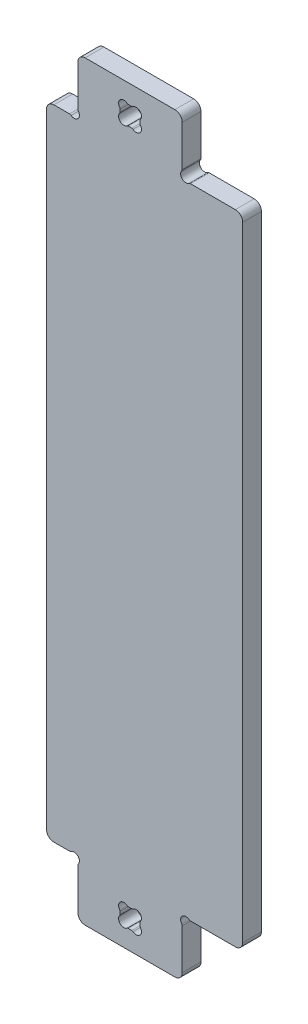
SolidWorks part; units mm, degrees
ref_plane "Plan de face" through (0, 0, 0) normal (0, 0, 1) x (1, 0, 0)
ref_plane "Plan de dessus" through (0, 0, 0) normal (0, 1, 0) x (1, 0, 0)
ref_plane "Plan de droite" through (0, 0, 0) normal (1, 0, 0) x (0, 0, -1)
sketch "Esquisse2" plane through (0, 0, 0) normal (0, 0, 1) x (1, 0, 0)
  line L0 (0, 54) -> (-3.6998, 50.3002) construction
  line L1 (0, 0) -> (100, 0)
  line L2 (0, 0) -> (0, 46.0122)
  line L3 (157.9949, 618.7663) -> (157.9949, 101.2337) construction
  line L4 (100, 0) -> (100, 46.0122)
  line L5 (157.9949, 360) -> (-30, 360)
  line L6 (100, 54) -> (107.0711, 46.9289) construction
  line L7 (-7.9878, 54) -> (-30, 54)
  line L8 (-30, 360) -> (-30, 54)
  line L11 (107.9878, 54) -> (157.9949, 54)
  line L12 (157.9949, 360) -> (157.9949, 54)
  arc A0 (0.4882, 47.4963) -> (-6.5037, 54.4882) centre (-3.5355, 50.4645) ccw
  arc A1 (106.5037, 54.4882) -> (99.5118, 47.4963) centre (103.5355, 50.4645) ccw
  arc A2 (-6.5037, 54.4882) -> (-7.9878, 54) centre (-7.9878, 56.5) cw
  arc A3 (0, 46.0122) -> (0.4882, 47.4963) centre (2.5, 46.0122) cw
  arc A4 (106.5037, 54.4882) -> (107.9878, 54) centre (107.9878, 56.5) ccw
  arc A5 (100, 46.0122) -> (99.5118, 47.4963) centre (97.5, 46.0122) ccw
  dimension "D3" = 45
  dimension "D4" = 5
  dimension "D8" = 2.5
  dimension "D1" = 100
  dimension "D5" = 45
  dimension "D2" = 360
  dimension "D6" = 54
  dimension "D7" = 30
extrude "Boss.-Extru.2" add sketch "Esquisse2" along normal blind 18
sketch "Esquisse1" plane through (0, 0, 0) normal (0, 0, 1) x (1, 0, 0)
  line L0 (50, 0) -> (50, 18) construction
  line L1 (0, 0) -> (100, 0) construction
  line L3 (59.5, 28.2488) -> (59.5, 25.7512)
  line L4 (48.2512, 36) -> (51.7488, 36)
  line L5 (40.5, 27) -> (59.5, 27) construction
  line L6 (40.5, 28.2488) -> (40.5, 25.7512)
  line L7 (48.2512, 18) -> (51.7488, 18)
  line L8 (-30, 54) -> (-7.9878, 54) construction
  line L9 (40.5, 18) -> (50, 27.5) construction
  arc A0 (40.1123, 24.6353) -> (47.1353, 17.6123) centre (44.0355, 21.5355) ccw
  arc A1 (52.8647, 17.6123) -> (51.7488, 18) centre (51.7488, 16.2) ccw
  arc A2 (59.8877, 24.6353) -> (52.8647, 17.6123) centre (55.9645, 21.5355) cw
  arc A3 (59.8877, 24.6353) -> (59.5, 25.7512) centre (61.3, 25.7512) cw
  arc A4 (40.1123, 24.6353) -> (40.5, 25.7512) centre (38.7, 25.7512) ccw
  arc A5 (47.1353, 17.6123) -> (48.2512, 18) centre (48.2512, 16.2) cw
  arc A6 (59.8877, 29.3647) -> (59.5, 28.2488) centre (61.3, 28.2488) ccw
  arc A7 (59.8877, 29.3647) -> (52.8647, 36.3877) centre (55.9645, 32.4645) ccw
  arc A8 (52.8647, 36.3877) -> (51.7488, 36) centre (51.7488, 37.8) cw
  arc A9 (47.1353, 36.3877) -> (48.2512, 36) centre (48.2512, 37.8) ccw
  arc A10 (40.1123, 29.3647) -> (47.1353, 36.3877) centre (44.0355, 32.4645) cw
  arc A11 (40.1123, 29.3647) -> (40.5, 28.2488) centre (38.7, 28.2488) cw
  point P2 (50, 0)
  point P21 (50, 18)
  point P32 (40.5, 25.0711)
  point P35 (47.5711, 18)
  dimension "D1" = 18
  dimension "D7" = 5
  dimension "D2" = 1.8
  dimension "D3" = 45
  dimension "D5" = 9
  dimension "D6" = 9.5
extrude "Enlèv. mat.-Extru.1" cut sketch "Esquisse1" along normal through all
fillet "Congé1" radius 7 4 edges at (100, 0, 9) (0, 0, 9) (-30, 54, 9) (157.9949, 54, 9)
mirror "Symétrie1" about plane through (157.9949, 360, 18) normal (0, -1, 0) of bodies 104
equation "\"tool_diameter\"=9"
equation "\"D1@Boss.-Extru.2\" = \"material_thickness\""
equation "\"D7@Esquisse1\"=\"tool_diameter\"/2+\"hole_clearance\""
equation "\"D6@Esquisse1\" = \"material_thickness\" / 2 + \"clearance\""
equation "\"fillet\"=7"
equation "\"D5@Esquisse1\" = \"material_thickness\" / 2"
equation "\"D4@Esquisse2\"=\"tool_diameter\"/2+\"hole_clearance\""
equation "\"D1@Esquisse1\" = \"material_thickness\""
equation "\"D1@Congé1\"=\"fillet\""
equation "\"clearance\"=0.5"
equation "\"D6@Esquisse2\"= \"material_thickness\" * 3"
equation "\"outer_slot\"=0.5"
equation "\"hole_clearance\"=0.5"
equation "\"material_thickness\"=18"
equation "\"D8@Esquisse2\"=\"D4@Esquisse2\"/2"
equation "\"D2@Esquisse1\"=\"material_thickness\"/10"
equation "\"string\"= 2 * \"tool_diameter\" / 2 * cos ( 45deg )"
equation "\"angle\"= IIF ( \"string\" < \"limit\" , 45 , ( 180 - 2 * arcsin ( \"ThicknessVStool_dia\" ) ) / 2 )"
equation "\"limit\"= \"material_thickness\" / 2 * 9 / 10"
equation "\"ThicknessVStool_dia\"= IIF ( \"limit\" / \"tool_diameter\" > 1 , 1 , \"limit\" / \"tool_diameter\" )"
equation "\"D3@Esquisse1\"=\"angle\""
